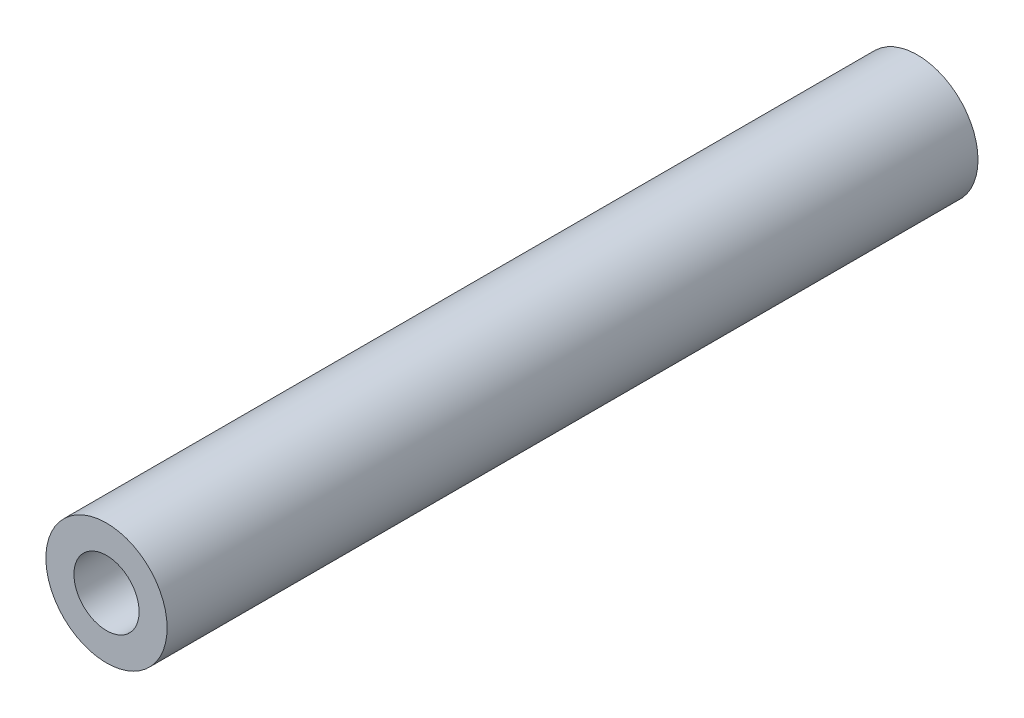
SolidWorks part; units mm, degrees
ref_plane "Front Plane" through (0, 0, 0) normal (0, 0, 1) x (1, 0, 0)
ref_plane "Top Plane" through (0, 0, 0) normal (0, 1, 0) x (1, 0, 0)
ref_plane "Right Plane" through (0, 0, 0) normal (1, 0, 0) x (0, 0, -1)
sketch "Sketch1" plane through (0, 0, 0) normal (0, 0, 1) x (1, 0, 0)
  circle A0 centre (0, 0) radius 2.15
  circle A1 centre (0, 0) radius 4
  dimension "D1" = 4.3
  dimension "D2" = 8
extrude "Boss-Extrude1" add sketch "Sketch1" along normal blind 53.5
